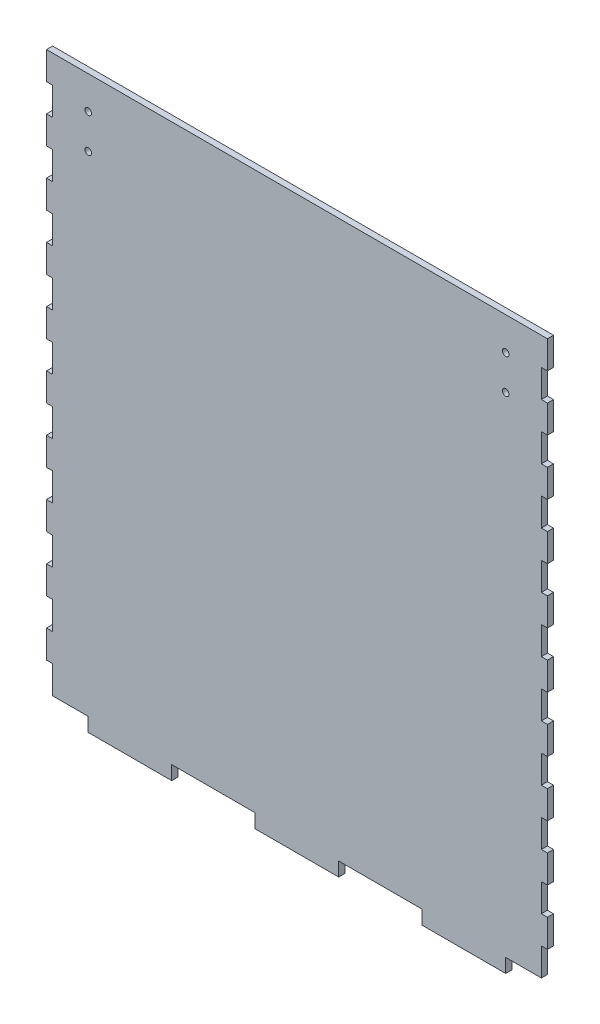
SolidWorks part; units mm, degrees
material "Acrylic (Medium-high impact)"
ref_plane "Front Plane" through (0, 0, 0) normal (0, 0, 1) x (1, 0, 0)
ref_plane "Top Plane" through (0, 0, 0) normal (0, 1, 0) x (1, 0, 0)
ref_plane "Right Plane" through (0, 0, 0) normal (1, 0, 0) x (0, 0, -1)
sketch "Sketch1" plane through (0, 0, 0) normal (0, 0, 1) x (1, 0, 0)
  line L0 (-114.3, 114.3) -> (-111.5219, 114.3)
  line L1 (-114.3, 127) -> (114.3, 127)
  line L2 (-114.3, 127) -> (-114.3, -127)
  line L3 (-114.3, -127) -> (114.3, -127)
  line L4 (114.3, 127) -> (114.3, -127)
  line L5 (-114.3, 127) -> (-111.5219, 127)
  line L6 (-114.3, 127) -> (-114.3, 114.3)
  line L7 (-114.3, 114.3) -> (-111.5219, 114.3)
  line L8 (-111.5219, 127) -> (-111.5219, 114.3)
  line L9 (-114.3, 114.3) -> (-114.3, 101.6)
  line L10 (-114.3, 101.6) -> (-111.5219, 101.6)
  line L11 (-111.5219, 114.3) -> (-111.5219, 101.6)
  line L12 (-114.3, 101.6) -> (-111.5219, 101.6)
  line L13 (-114.3, 101.6) -> (-114.3, 88.9)
  line L14 (-114.3, 88.9) -> (-111.5219, 88.9)
  line L15 (-111.5219, 101.6) -> (-111.5219, 88.9)
  line L16 (-114.3, 88.9) -> (-111.5219, 88.9)
  line L17 (-114.3, 88.9) -> (-114.3, 76.2)
  line L18 (-114.3, 76.2) -> (-111.5219, 76.2)
  line L19 (-111.5219, 88.9) -> (-111.5219, 76.2)
  line L20 (-114.3, 76.2) -> (-111.5219, 76.2)
  line L21 (-114.3, 76.2) -> (-114.3, 63.5)
  line L22 (-114.3, 63.5) -> (-111.5219, 63.5)
  line L23 (-111.5219, 76.2) -> (-111.5219, 63.5)
  line L24 (-114.3, 63.5) -> (-111.5219, 63.5)
  line L25 (-114.3, 63.5) -> (-114.3, 50.8)
  line L26 (-114.3, 50.8) -> (-111.5219, 50.8)
  line L27 (-111.5219, 63.5) -> (-111.5219, 50.8)
  line L28 (-114.3, 50.8) -> (-111.5219, 50.8)
  line L29 (-114.3, 50.8) -> (-114.3, 38.1)
  line L30 (-114.3, 38.1) -> (-111.5219, 38.1)
  line L31 (-111.5219, 50.8) -> (-111.5219, 38.1)
  line L32 (-114.3, 38.1) -> (-111.5219, 38.1)
  line L33 (-114.3, 38.1) -> (-114.3, 25.4)
  line L34 (-114.3, 25.4) -> (-111.5219, 25.4)
  line L35 (-111.5219, 38.1) -> (-111.5219, 25.4)
  line L36 (-114.3, 25.4) -> (-111.5219, 25.4)
  line L37 (-114.3, 25.4) -> (-114.3, 12.7)
  line L38 (-114.3, 12.7) -> (-111.5219, 12.7)
  line L39 (-111.5219, 25.4) -> (-111.5219, 12.7)
  line L40 (-114.3, 12.7) -> (-111.5219, 12.7)
  line L41 (-114.3, 12.7) -> (-114.3, 0)
  line L42 (-114.3, 0) -> (-111.5219, 0)
  line L43 (-111.5219, 12.7) -> (-111.5219, 0)
  line L44 (-114.3, 0) -> (-111.5219, 0)
  line L45 (-114.3, 0) -> (-114.3, -12.7)
  line L46 (-114.3, -12.7) -> (-111.5219, -12.7)
  line L47 (-111.5219, 0) -> (-111.5219, -12.7)
  line L48 (-114.3, -12.7) -> (-111.5219, -12.7)
  line L49 (-114.3, -12.7) -> (-114.3, -25.4)
  line L50 (-114.3, -25.4) -> (-111.5219, -25.4)
  line L51 (-111.5219, -12.7) -> (-111.5219, -25.4)
  line L52 (-114.3, -25.4) -> (-111.5219, -25.4)
  line L53 (-114.3, -25.4) -> (-114.3, -38.1)
  line L54 (-114.3, -38.1) -> (-111.5219, -38.1)
  line L55 (-111.5219, -25.4) -> (-111.5219, -38.1)
  line L56 (-114.3, -38.1) -> (-111.5219, -38.1)
  line L57 (-114.3, -38.1) -> (-114.3, -50.8)
  line L58 (-114.3, -50.8) -> (-111.5219, -50.8)
  line L59 (-111.5219, -38.1) -> (-111.5219, -50.8)
  line L60 (-114.3, -50.8) -> (-111.5219, -50.8)
  line L61 (-114.3, -50.8) -> (-114.3, -63.5)
  line L62 (-114.3, -63.5) -> (-111.5219, -63.5)
  line L63 (-111.5219, -50.8) -> (-111.5219, -63.5)
  line L64 (-114.3, -63.5) -> (-111.5219, -63.5)
  line L65 (-114.3, -63.5) -> (-114.3, -76.2)
  line L66 (-114.3, -76.2) -> (-111.5219, -76.2)
  line L67 (-111.5219, -63.5) -> (-111.5219, -76.2)
  line L68 (-114.3, -76.2) -> (-111.5219, -76.2)
  line L69 (-114.3, -76.2) -> (-114.3, -88.9)
  line L70 (-114.3, -88.9) -> (-111.5219, -88.9)
  line L71 (-111.5219, -76.2) -> (-111.5219, -88.9)
  line L72 (-114.3, -88.9) -> (-111.5219, -88.9)
  line L73 (-114.3, -88.9) -> (-114.3, -101.6)
  line L74 (-114.3, -101.6) -> (-111.5219, -101.6)
  line L75 (-111.5219, -88.9) -> (-111.5219, -101.6)
  line L76 (-114.3, -101.6) -> (-111.5219, -101.6)
  line L77 (-114.3, -101.6) -> (-114.3, -114.3)
  line L78 (-114.3, -114.3) -> (-111.5219, -114.3)
  line L79 (-111.5219, -101.6) -> (-111.5219, -114.3)
  line L80 (-114.3, -114.3) -> (-111.5219, -114.3)
  line L81 (-114.3, -114.3) -> (-114.3, -127)
  line L82 (-114.3, -127) -> (-111.5219, -127)
  line L83 (-111.5219, -114.3) -> (-111.5219, -127)
  line L100 (0, 127) -> (0, -127) construction
  line L101 (114.3, 114.3) -> (111.5219, 114.3)
  line L102 (114.3, 127) -> (111.5219, 127)
  line L103 (114.3, 127) -> (114.3, 114.3)
  line L104 (114.3, 114.3) -> (111.5219, 114.3)
  line L105 (111.5219, 127) -> (111.5219, 114.3)
  line L106 (114.3, 114.3) -> (114.3, 101.6)
  line L107 (114.3, 101.6) -> (111.5219, 101.6)
  line L108 (111.5219, 114.3) -> (111.5219, 101.6)
  line L109 (114.3, 101.6) -> (111.5219, 101.6)
  line L110 (114.3, 101.6) -> (114.3, 88.9)
  line L111 (114.3, 88.9) -> (111.5219, 88.9)
  line L112 (111.5219, 101.6) -> (111.5219, 88.9)
  line L113 (114.3, 88.9) -> (111.5219, 88.9)
  line L114 (114.3, 88.9) -> (114.3, 76.2)
  line L115 (114.3, 76.2) -> (111.5219, 76.2)
  line L116 (111.5219, 88.9) -> (111.5219, 76.2)
  line L117 (114.3, 76.2) -> (111.5219, 76.2)
  line L118 (114.3, 76.2) -> (114.3, 63.5)
  line L119 (114.3, 63.5) -> (111.5219, 63.5)
  line L120 (111.5219, 76.2) -> (111.5219, 63.5)
  line L121 (114.3, 63.5) -> (111.5219, 63.5)
  line L122 (114.3, 63.5) -> (114.3, 50.8)
  line L123 (114.3, 50.8) -> (111.5219, 50.8)
  line L124 (111.5219, 63.5) -> (111.5219, 50.8)
  line L125 (114.3, 50.8) -> (111.5219, 50.8)
  line L126 (114.3, 50.8) -> (114.3, 38.1)
  line L127 (114.3, 38.1) -> (111.5219, 38.1)
  line L128 (111.5219, 50.8) -> (111.5219, 38.1)
  line L129 (114.3, 38.1) -> (111.5219, 38.1)
  line L130 (114.3, 38.1) -> (114.3, 25.4)
  line L131 (114.3, 25.4) -> (111.5219, 25.4)
  line L132 (111.5219, 38.1) -> (111.5219, 25.4)
  line L133 (114.3, 25.4) -> (111.5219, 25.4)
  line L134 (114.3, 25.4) -> (114.3, 12.7)
  line L135 (114.3, 12.7) -> (111.5219, 12.7)
  line L136 (111.5219, 25.4) -> (111.5219, 12.7)
  line L137 (114.3, 12.7) -> (111.5219, 12.7)
  line L138 (114.3, 12.7) -> (114.3, 0)
  line L139 (114.3, 0) -> (111.5219, 0)
  line L140 (111.5219, 12.7) -> (111.5219, 0)
  line L141 (114.3, 0) -> (111.5219, 0)
  line L142 (114.3, 0) -> (114.3, -12.7)
  line L143 (114.3, -12.7) -> (111.5219, -12.7)
  line L144 (111.5219, 0) -> (111.5219, -12.7)
  line L145 (114.3, -12.7) -> (111.5219, -12.7)
  line L146 (114.3, -12.7) -> (114.3, -25.4)
  line L147 (114.3, -25.4) -> (111.5219, -25.4)
  line L148 (111.5219, -12.7) -> (111.5219, -25.4)
  line L149 (114.3, -25.4) -> (111.5219, -25.4)
  line L150 (114.3, -25.4) -> (114.3, -38.1)
  line L151 (114.3, -38.1) -> (111.5219, -38.1)
  line L152 (111.5219, -25.4) -> (111.5219, -38.1)
  line L153 (114.3, -38.1) -> (111.5219, -38.1)
  line L154 (114.3, -38.1) -> (114.3, -50.8)
  line L155 (114.3, -50.8) -> (111.5219, -50.8)
  line L156 (111.5219, -38.1) -> (111.5219, -50.8)
  line L157 (114.3, -50.8) -> (111.5219, -50.8)
  line L158 (114.3, -50.8) -> (114.3, -63.5)
  line L159 (114.3, -63.5) -> (111.5219, -63.5)
  line L160 (111.5219, -50.8) -> (111.5219, -63.5)
  line L161 (114.3, -63.5) -> (111.5219, -63.5)
  line L162 (114.3, -63.5) -> (114.3, -76.2)
  line L163 (114.3, -76.2) -> (111.5219, -76.2)
  line L164 (111.5219, -63.5) -> (111.5219, -76.2)
  line L165 (114.3, -76.2) -> (111.5219, -76.2)
  line L166 (114.3, -76.2) -> (114.3, -88.9)
  line L167 (114.3, -88.9) -> (111.5219, -88.9)
  line L168 (111.5219, -76.2) -> (111.5219, -88.9)
  line L169 (114.3, -88.9) -> (111.5219, -88.9)
  line L170 (114.3, -88.9) -> (114.3, -101.6)
  line L171 (114.3, -101.6) -> (111.5219, -101.6)
  line L172 (111.5219, -88.9) -> (111.5219, -101.6)
  line L173 (114.3, -101.6) -> (111.5219, -101.6)
  line L174 (114.3, -101.6) -> (114.3, -114.3)
  line L175 (114.3, -114.3) -> (111.5219, -114.3)
  line L176 (111.5219, -101.6) -> (111.5219, -114.3)
  line L177 (114.3, -114.3) -> (111.5219, -114.3)
  line L178 (114.3, -114.3) -> (114.3, -127)
  line L179 (114.3, -127) -> (111.5219, -127)
  line L180 (111.5219, -114.3) -> (111.5219, -127)
  line L183 (95.25, -127) -> (95.25, -133.35)
  line L184 (95.25, -133.35) -> (57.15, -133.35)
  line L185 (57.15, -133.35) -> (57.15, -127)
  line L186 (57.15, -127) -> (95.25, -127)
  line L188 (-19.05, -127) -> (19.05, -127)
  line L189 (19.05, -127) -> (19.05, -133.35)
  line L190 (19.05, -133.35) -> (-19.05, -133.35)
  line L191 (-19.05, -133.35) -> (-19.05, -127)
  line L192 (-95.25, -127) -> (-57.15, -127)
  line L193 (-57.15, -127) -> (-57.15, -133.35)
  line L194 (-57.15, -133.35) -> (-95.25, -133.35)
  line L195 (-95.25, -133.35) -> (-95.25, -127)
  point P4 (0, 127)
  point P6 (-114.3, 0)
  dimension "D1" = 254
  dimension "D2" = 228.6
  dimension "D3" = 12.7
  dimension "D4" = 2.7781
  dimension "D7" = 6.35
  dimension "D8" = 38.1
  dimension "D9" = 19.05
  dimension "D11" = 19.05
  dimension "D5" = 20
  dimension "D6" = 20
  dimension "D10" = 3
extrude "Boss-Extrude1" add sketch "Sketch1" along normal blind 2.7781 contours L100 L1 L8 L11 L15 L19 L23 L27 L31 L35 L39 L43 L47 L51 L55 L59 L63 L67 L71 L75 L79 L83 L3 | L1 L100 L3 L180 L176 L172 L168 L164 L160 L156 L152 L148 L144 L140 L136 L132 L128 L124 L120 L116 L112 L108 L105 | L1 L105 L101 L4 | L107 L112 L111 L4 | L115 L120 L119 L4 | L123 L128 L127 L4 | L131 L136 L135 L4 | L139 L144 L143 L4 | L147 L152 L151 L4 | L155 L160 L159 L4 | L163 L168 L167 L4 | L171 L176 L175 L4 | L8 L1 L2 L0 | L15 L10 L2 L14 | L23 L18 L2 L22 | L31 L26 L2 L30 | L63 L58 L2 L62 | L71 L66 L2 L70 | L79 L74 L2 L78 | L185 L184 L183 L3 | L191 L190 L189 L188 L3 | L195 L194 L193 L3
sketch "Sketch2" plane through (0, 0, 0) normal (0, 0, -1) x (-1, 0, 0)
  line L0 (-114.3, 127) -> (-114.3, 114.3) construction
  line L1 (114.3, 127) -> (-114.3, 127) construction
  line L2 (0, 127) -> (0, -133.35) construction
  line L3 (-19.05, -133.35) -> (19.05, -133.35) construction
  circle A0 centre (-95.25, 112) radius 1.5
  circle A1 centre (-95.25, 96.25) radius 1.5
  circle A2 centre (95.25, 96.25) radius 1.5
  circle A3 centre (95.25, 112) radius 1.5
  dimension "D1" = 3
  dimension "D2" = 3
  dimension "D3" = 15.75
  dimension "D4" = 19.05
  dimension "D5" = 15
extrude "Cut-Extrude1" cut sketch "Sketch2" against normal up to surface (2.7781 mm away) up to face at (0, -16.9793, 2.7781)
equation "\"wall_thickness\" = 7/64in"
equation "\"base_thickness\" = 0.25in"
equation "\"D4@Sketch1\"=\"wall_thickness\""
equation "\"D7@Sketch1\"=\"base_thickness\""
equation "\"D1@Boss-Extrude1\"=\"wall_thickness\""
